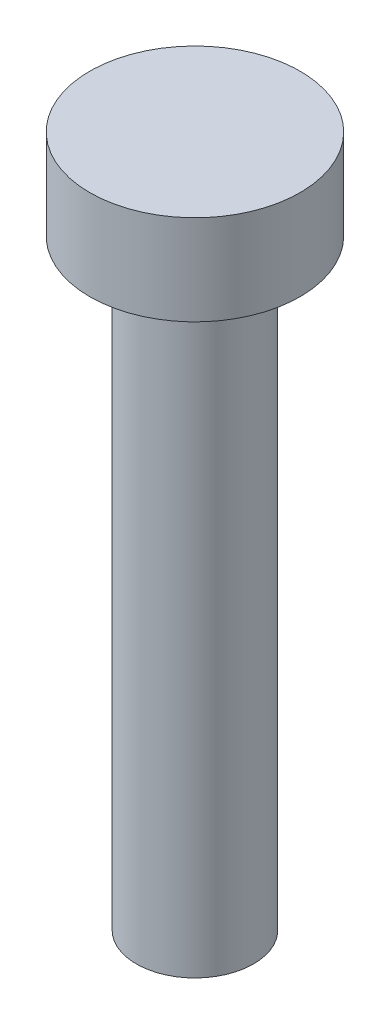
SolidWorks part; units mm, degrees
ref_plane "Front Plane" through (0, 0, 0) normal (0, 0, 1) x (1, 0, 0)
ref_plane "Top Plane" through (0, 0, 0) normal (0, 1, 0) x (1, 0, 0)
ref_plane "Right Plane" through (0, 0, 0) normal (1, 0, 0) x (0, 0, -1)
sketch "Sketch1" plane through (0, 0, 0) normal (0, 1, 0) x (1, 0, 0)
  circle A0 centre (0, 0) radius 3.5
  dimension "D1" = 7
extrude "Boss-Extrude1" add sketch "Sketch1" along normal blind 3
sketch "Sketch2" plane through (0, 0, 0) normal (0, -1, 0) x (1, 0, 0)
  circle A0 centre (0, 0) radius 1.95
  dimension "D1" = 3.9
extrude "Boss-Extrude2" add sketch "Sketch2" along normal blind 20
